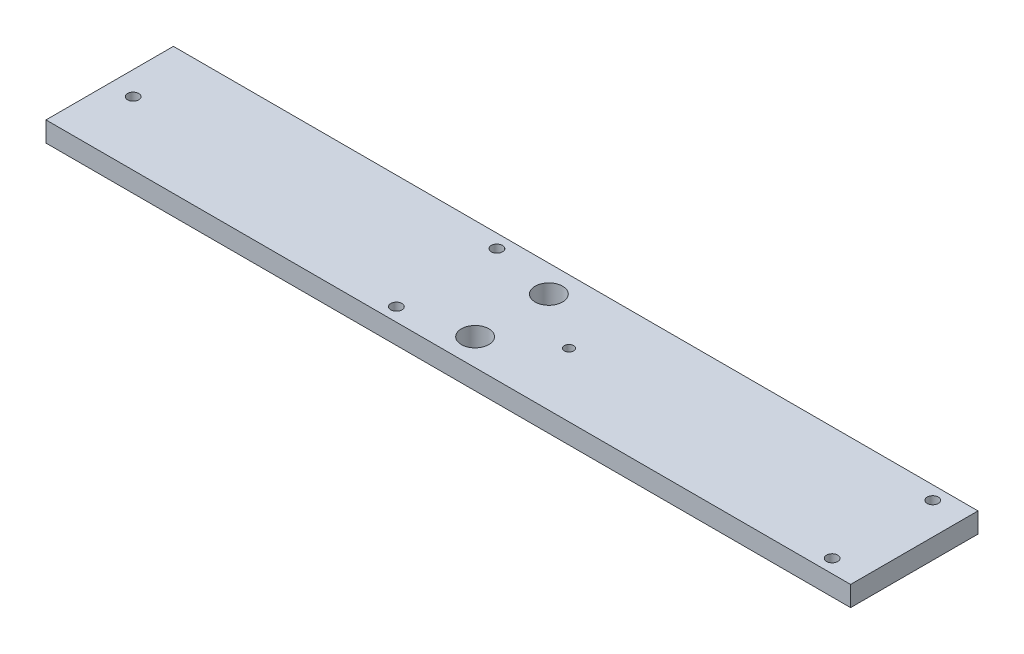
SolidWorks part; units mm, degrees
ref_plane "Front Plane" through (0, 0, 0) normal (0, 0, 1) x (1, 0, 0)
ref_plane "Top Plane" through (0, 0, 0) normal (0, 1, 0) x (1, 0, 0)
ref_plane "Right Plane" through (0, 0, 0) normal (1, 0, 0) x (0, 0, -1)
sketch "Sketch1" plane through (0, 0, 0) normal (0, 1, 0) x (1, 0, 0)
  line L1 (0, 0) -> (120, 0)
  line L2 (0, 0) -> (0, 19)
  line L3 (0, 19) -> (120, 19)
  line L4 (120, 0) -> (120, 19)
  dimension "D1" = 19
  dimension "D2" = 120
extrude "Boss-Extrude1" add sketch "Sketch1" along normal blind 3
sketch "Sketch2" plane through (0, 3, 0) normal (0, 1, 0) x (1, 0, 0)
  line L0 (0, 19) -> (0, 0) construction
  line L1 (55, 19) -> (55, 0) construction
  line L2 (120, 19) -> (0, 19) construction
  line L3 (0, 0) -> (120, 0) construction
  line L4 (65, 19) -> (65, 0) construction
  line L5 (120, 0) -> (120, 19) construction
  circle A0 centre (3.5, 9.5) radius 0.835
  circle A1 centre (50.25, 17) radius 0.835
  circle A2 centre (50.25, 2) radius 0.835
  circle A3 centre (68.5, 9.5) radius 0.6943
  circle A4 centre (115.25, 17) radius 0.835
  circle A5 centre (115.25, 2) radius 0.835
  circle A6 centre (60, 15) radius 2.05
  circle A7 centre (60, 4) radius 2.05
  point P24 (0, 9.5)
  point P29 (60, 19)
  dimension "D13" = 1.67
  dimension "D14" = 1.67
  dimension "D15" = 1.67
  dimension "D16" = 1.67
  dimension "D17" = 1.67
  dimension "D18" = 4.1
  dimension "D19" = 4.1
  dimension "D1" = 3.5
  dimension "D2" = 55
  dimension "D3" = 55
  dimension "D4" = 4.75
  dimension "D5" = 4.75
  dimension "D6" = 3.5
  dimension "D7" = 4.75
  dimension "D8" = 4.75
  dimension "D9" = 2
  dimension "D10" = 2
  dimension "D11" = 2
  dimension "D12" = 2
  dimension "D20" = 4
  dimension "D21" = 4
extrude "Cut-Extrude1" cut sketch "Sketch2" against normal through all
